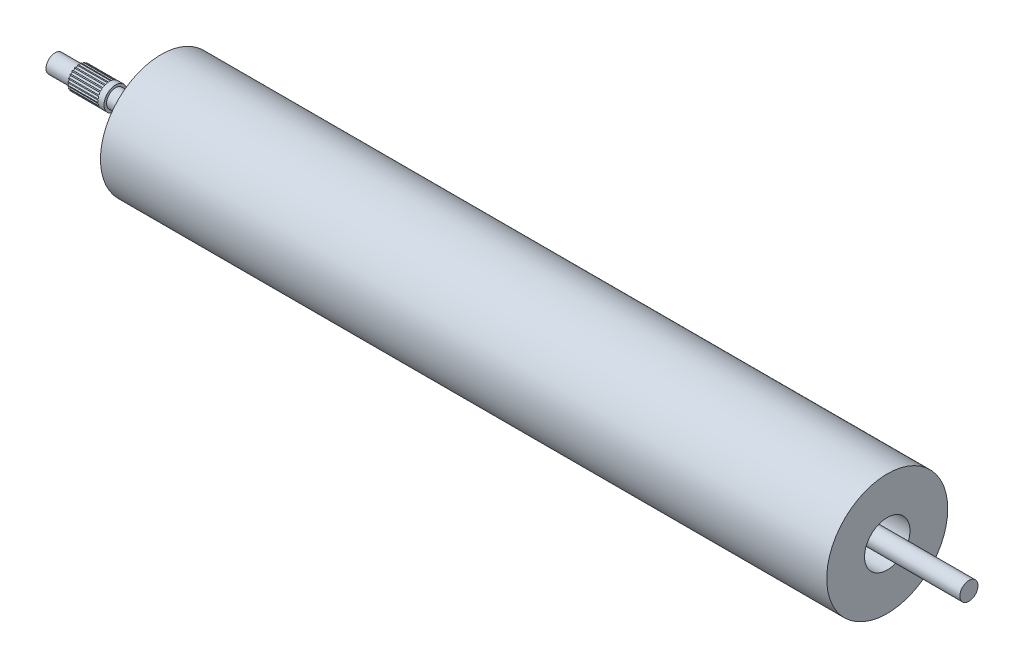
SolidWorks part; units mm, degrees
ref_plane "Front Plane" through (0, 0, 0) normal (0, 0, 1) x (1, 0, 0)
ref_plane "Top Plane" through (0, 0, 0) normal (0, 1, 0) x (1, 0, 0)
ref_plane "Right Plane" through (0, 0, 0) normal (1, 0, 0) x (0, 0, -1)
sketch "Sketch1" plane through (0, 0, 0) normal (1, 0, 0) x (0, 0, -1)
  circle A0 centre (0, 0) radius 20
  circle A1 centre (0, 0) radius 7.5
extrude "Boss-Extrude1" add sketch "Sketch1" along normal blind 240
sketch "Sketch2" plane through (240, 0, 0) normal (1, 0, 0) x (0, 0, -1)
  line L0 (-13.75, 0) -> (-20, 0)
  line L1 (-8.2581, -10.9939) -> (-12.0118, -15.9911)
  circle A1 centre (0, 0) radius 20 construction
  arc A5 (-20, 0) -> (-12.1972, -15.8502) centre (0, 0) ccw
  arc A6 (-13.75, 0) -> (-8.2581, -10.9939) centre (0, 0) ccw
sketch "Sketch6" plane through (240, 0, 0) normal (1, 0, 0) x (0, 0, -1)
  circle A0 centre (0, 0) radius 3
extrude "Boss-Extrude2" add sketch "Sketch6" along normal blind 27 and the other way blind 275 separate body
ref_plane "Plane1" through (-15, 0, 0) normal (-1, 0, 0) x (0, 0, 1)
sketch "Sketch7" plane through (-15, 0, 0) normal (-1, 0, 0) x (0, 0, 1)
  circle A0 centre (0, 0) radius 20
  circle A1 centre (0, 0) radius 3.142
  circle A2 centre (0, 0) radius 3.8236
extrude "Boss-Extrude3" add sketch "Sketch7" along normal blind 12 contours A2
sketch "Sketch8" plane through (-27, 0, 0) normal (-1, 0, 0) x (0, 0, 1)
  circle A0 centre (-3.8236, 0) radius 0.3463
  circle A1 centre (0, 0) radius 3.8236 construction
  circle A2 centre (-3.6933, 0.9896) radius 0.3463
  circle A3 centre (-3.3114, 1.9118) radius 0.3463
  circle A4 centre (-2.7037, 2.7037) radius 0.3463
  circle A5 centre (-1.9118, 3.3114) radius 0.3463
  circle A6 centre (-0.9896, 3.6933) radius 0.3463
  circle A7 centre (0, 3.8236) radius 0.3463
  circle A8 centre (0.9896, 3.6933) radius 0.3463
  circle A9 centre (1.9118, 3.3114) radius 0.3463
  circle A10 centre (2.7037, 2.7037) radius 0.3463
  circle A11 centre (3.3114, 1.9118) radius 0.3463
  circle A12 centre (3.6933, 0.9896) radius 0.3463
  circle A13 centre (3.8236, 0) radius 0.3463
  circle A14 centre (3.6933, -0.9896) radius 0.3463
  circle A15 centre (3.3114, -1.9118) radius 0.3463
  circle A16 centre (2.7037, -2.7037) radius 0.3463
  circle A17 centre (1.9118, -3.3114) radius 0.3463
  circle A18 centre (0.9896, -3.6933) radius 0.3463
  circle A19 centre (0, -3.8236) radius 0.3463
  circle A20 centre (-0.9896, -3.6933) radius 0.3463
  circle A21 centre (-1.9118, -3.3114) radius 0.3463
  circle A22 centre (-2.7037, -2.7037) radius 0.3463
  circle A23 centre (-3.3114, -1.9118) radius 0.3463
  circle A24 centre (-3.6933, -0.9896) radius 0.3463
  point P52 (0, 0)
  dimension "D1" = 24
extrude "Cut-Extrude1" cut sketch "Sketch8" against normal blind 10
